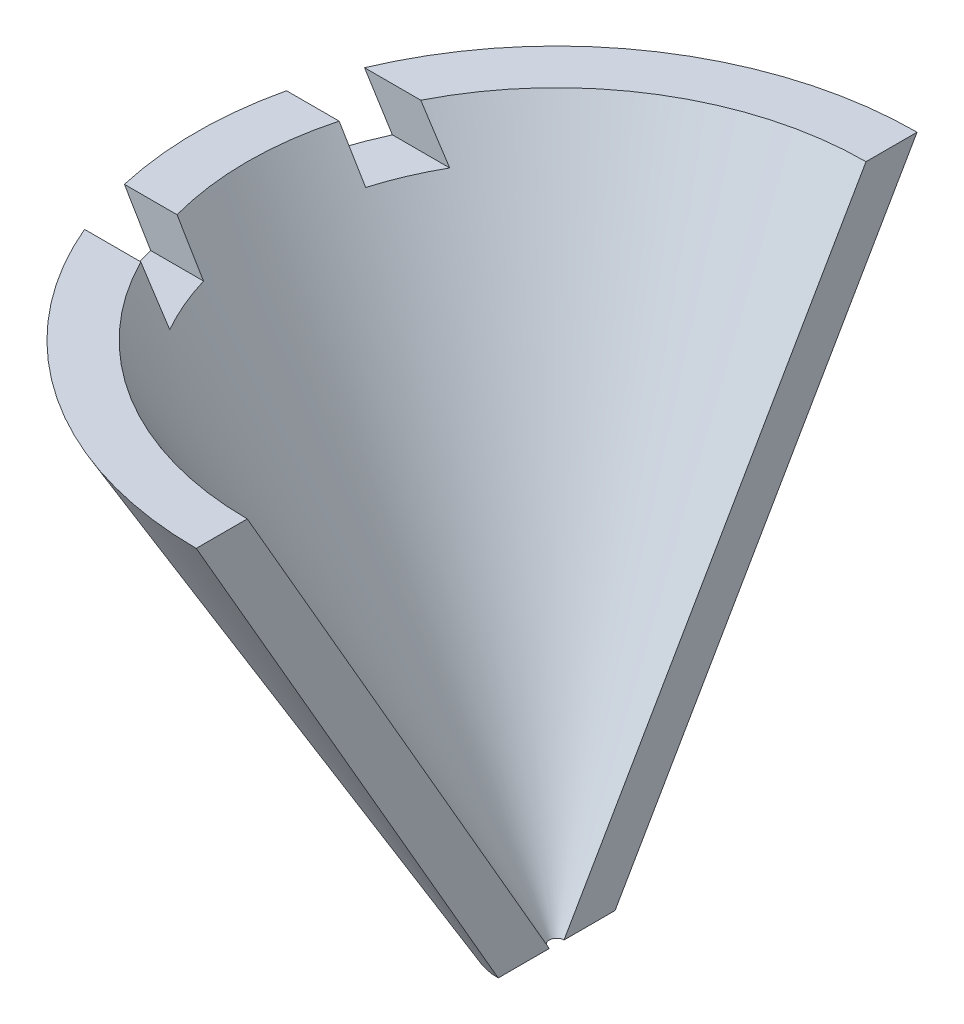
SolidWorks part; units mm, degrees
ref_plane "前视基准面" through (0, 0, 0) normal (0, 0, 1) x (1, 0, 0)
ref_plane "上视基准面" through (0, 0, 0) normal (0, 1, 0) x (1, 0, 0)
ref_plane "右视基准面" through (0, 0, 0) normal (1, 0, 0) x (0, 0, -1)
sketch "草图2" plane through (0, 0, 0) normal (0, 0, 1) x (1, 0, 0)
  line L0 (0, 0) -> (0, -34.2326) construction
  line L1 (-10.4966, 4.3243) -> (-12.2287, 4.3243)
  line L2 (0, 0) -> (-8, 0) construction
  line L3 (-12.2287, 4.3243) -> (-1.9821, -13.4234)
  line L4 (-1.9821, -13.4234) -> (-0.25, -13.4234)
  line L6 (-10.4966, 4.3243) -> (-0.25, -13.4234)
  circle A0 centre (-14, 9) radius 5 construction
  point P2 (0, 0)
  dimension "D1" = 60
  dimension "D2" = 8
  dimension "D3" = 1.5
  dimension "D4" = 0.5
revolve "旋转3" add sketch "草图2" angle 90 about L0
ref_plane "基准面4" through (0, 0, 2.75) normal (0, 0, 1) x (1, 0, 0)
sketch "草图4" plane through (0, 0, 2.75) normal (0, 0, 1) x (1, 0, 0)
  line L0 (0, 4.3243) -> (-12.2287, 4.3243) construction
  line L1 (-5.9154, 4.3243) -> (-11.9154, 4.3243)
  line L2 (-5.9154, 4.3243) -> (-5.9154, 2.8243)
  line L3 (-5.9154, 2.8243) -> (-11.9154, 2.8243)
  line L4 (-11.9154, 4.3243) -> (-11.9154, 2.8243)
  line L5 (0, 4.3243) -> (-10.4966, 4.3243) construction
  dimension "D1" = 1.5
  dimension "D2" = 6
extrude "切除-拉伸1" cut sketch "草图4" along normal blind 2
mirror "镜向1" about plane through (0, 0, 0) normal (0, 0, 1) of "切除-拉伸1"
